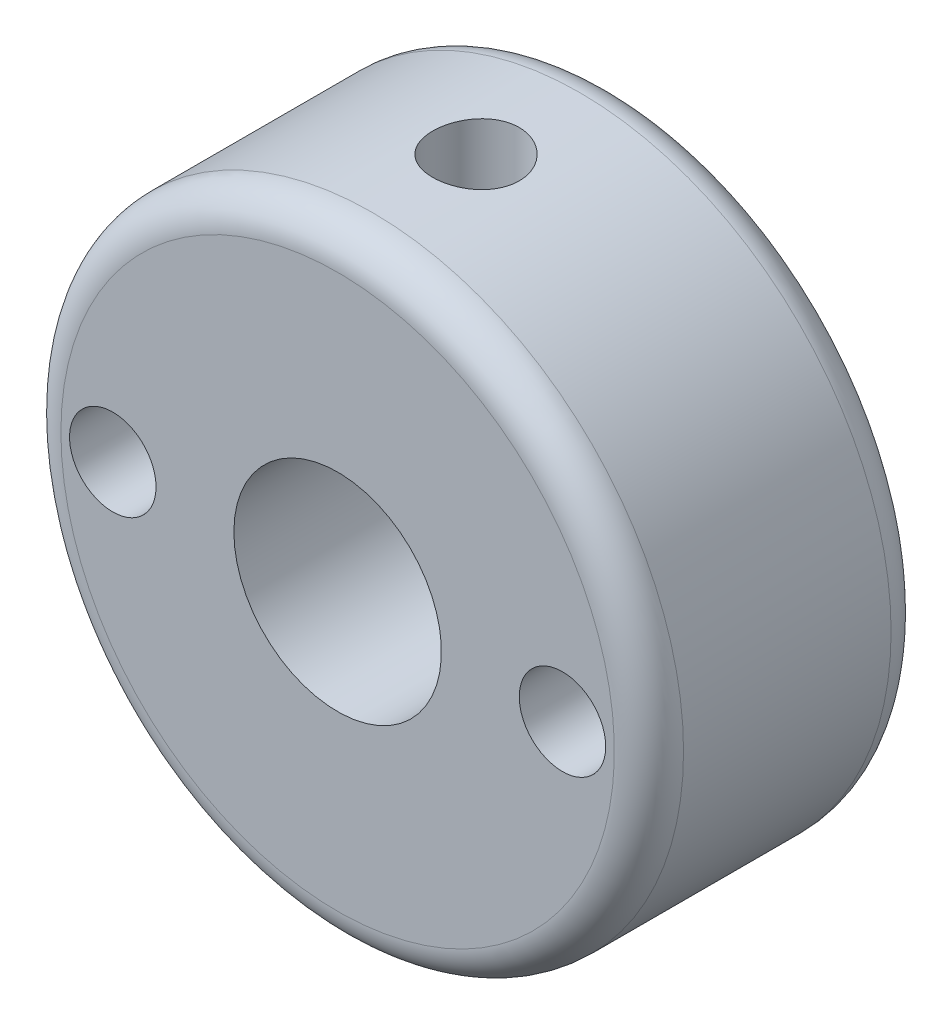
SolidWorks part; units mm, degrees
material "Malleable Cast Iron"
ref_plane "Front Plane" through (0, 0, 0) normal (0, 0, 1) x (1, 0, 0)
ref_plane "Top Plane" through (0, 0, 0) normal (0, 1, 0) x (1, 0, 0)
ref_plane "Right Plane" through (0, 0, 0) normal (1, 0, 0) x (0, 0, -1)
sketch "Sketch1" plane through (0, 0, 0) normal (0, 0, 1) x (1, 0, 0)
  line L1 (-9, -9) -> (9, -9)
  line L2 (-9, -9) -> (-9, 9)
  line L3 (-9, 9) -> (9, 9)
  line L4 (9, -9) -> (9, 9)
  line L5 (-9, -9) -> (9, 9) construction
  line L6 (-9, 9) -> (9, -9) construction
  point P0 (0, 0)
  dimension "D1" = 18
  dimension "D2" = 18
  dimension "D3" = 0
extrude "Boss-Extrude1" add sketch "Sketch1" along normal blind 8
hole_wizard "M3 Tapped Hole1" positions "Sketch6" profile "Sketch8" tap size "M3" standard "ISO" end condition through all
sketch "Sketch6" plane through (0, 0, 8) normal (0, 0, 1) x (1, 0, 0)
  point P0 (6.5, 0)
  point P2 (-6.5, 0)
  dimension "D1" = 6.5
  dimension "D2" = 6.5
cosmetic thread "Hole Thread2" parameters "D2"=3
cosmetic thread "Hole Thread3" parameters "D2"=3
sketch "Sketch8" plane through (6.5, 0, 8) normal (1, 0, 0) x (0, -1, 0)
  line L0 (0, 0) -> (0, 8)
  line L1 (0, 8) -> (1.25, 8)
  line L2 (1.25, 8) -> (1.25, 0)
  line L5 (1.25, 0) -> (0, 0)
  line L11 (0, -6.35) -> (0, 107.95) construction
  dimension "Thru Tap Drill Dia." = 2.5
  dimension "Thru Tap Drill Depth" = 8
hole_wizard "Ø6.0 (6) Diameter Hole1" positions "Sketch9" profile "Sketch11" hole size "Ø6.0" standard "ISO" end condition through all
sketch "Sketch9" plane through (0, 0, 0) normal (0, 0, -1) x (-1, 0, 0)
  point P0 (0, 0)
  dimension "D1" = 0
sketch "Sketch11" plane through (0, 0, 0) normal (1, 0, 0) x (0, 1, 0)
  line L0 (0, 0) -> (0, 8)
  line L1 (0, 8) -> (3, 8)
  line L2 (3, 8) -> (3, 0)
  line L5 (3, 0) -> (0, 0)
  line L11 (0, -6.35) -> (0, 107.95) construction
  dimension "Thru Hole Dia." = 6
  dimension "Thru Hole Depth" = 8
hole_wizard "M3 Tapped Hole2" positions "Sketch12" profile "Sketch14" tap size "M3" standard "ISO"
sketch "Sketch12" plane through (0, 9, 0) normal (0, 1, 0) x (1, 0, 0)
  line L0 (9, 0) -> (-9, 0) construction
  point P0 (0, -4)
  dimension "D1" = 4
sketch "Sketch14" plane through (0, 9, 4) normal (1, 0, 0) x (0, 0, 1)
  line L0 (0, 0) -> (0, 6)
  line L1 (0, 6) -> (1.25, 6)
  line L2 (1.25, 6) -> (1.25, 0)
  line L5 (1.25, 0) -> (0, 0)
  line L11 (0, -6.35) -> (0, 107.95) construction
  dimension "Thru Tap Drill Dia." = 2.5
  dimension "Thru Tap Drill Depth" = 6
cosmetic thread "Hole Thread4" parameters "D2"=3
sketch "Sketch15" plane through (0, 0, 8) normal (0, 0, 1) x (1, 0, 0)
  circle A0 centre (0, 0) radius 9
  circle A1 centre (0, 0) radius 12.7279
  dimension "D1" = 18
extrude "Cut-Extrude1" cut sketch "Sketch15" against normal blind 10
fillet "Fillet1" radius 1 2 edges at (-9, 0, 0) (9, 0, 8)
